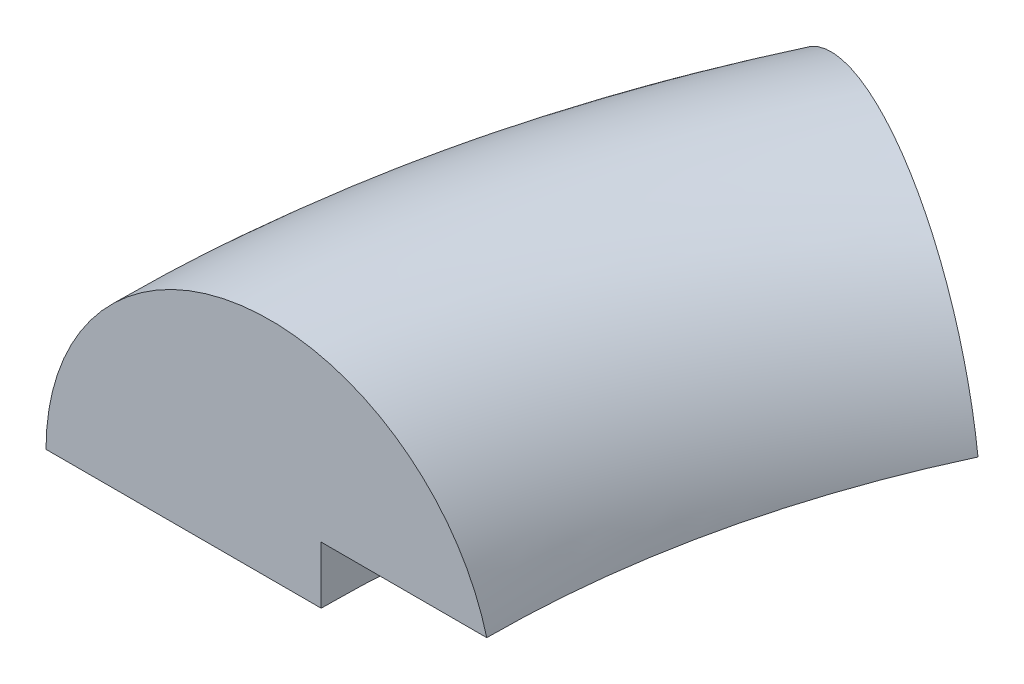
SolidWorks part; units mm, degrees
ref_plane "Front Plane" through (0, 0, 0) normal (0, 0, 1) x (1, 0, 0)
ref_plane "Top Plane" through (0, 0, 0) normal (0, 1, 0) x (1, 0, 0)
ref_plane "Right Plane" through (0, 0, 0) normal (1, 0, 0) x (0, 0, -1)
sketch "Sketch3" plane through (0, 0, 0) normal (0, 0, 1) x (1, 0, 0)
  line L1 (-25.3, 0) -> (-20.3, 0)
  line L2 (-20.3, 0) -> (-20.3, 1.0408)
  line L3 (-20.3, 1.0408) -> (-17.2904, 1.0408)
  line L4 (0, 5.059) -> (0, -7.856) construction
  arc A0 (-25.3, 0) -> (-17.2904, 1.0408) centre (-21.2276, 0) cw
  dimension "D4" = 4.0724
  dimension "D1" = 20.3
  dimension "D3" = 25.3
revolve "Revolve1" add sketch "Sketch3" angle 25 about L4
